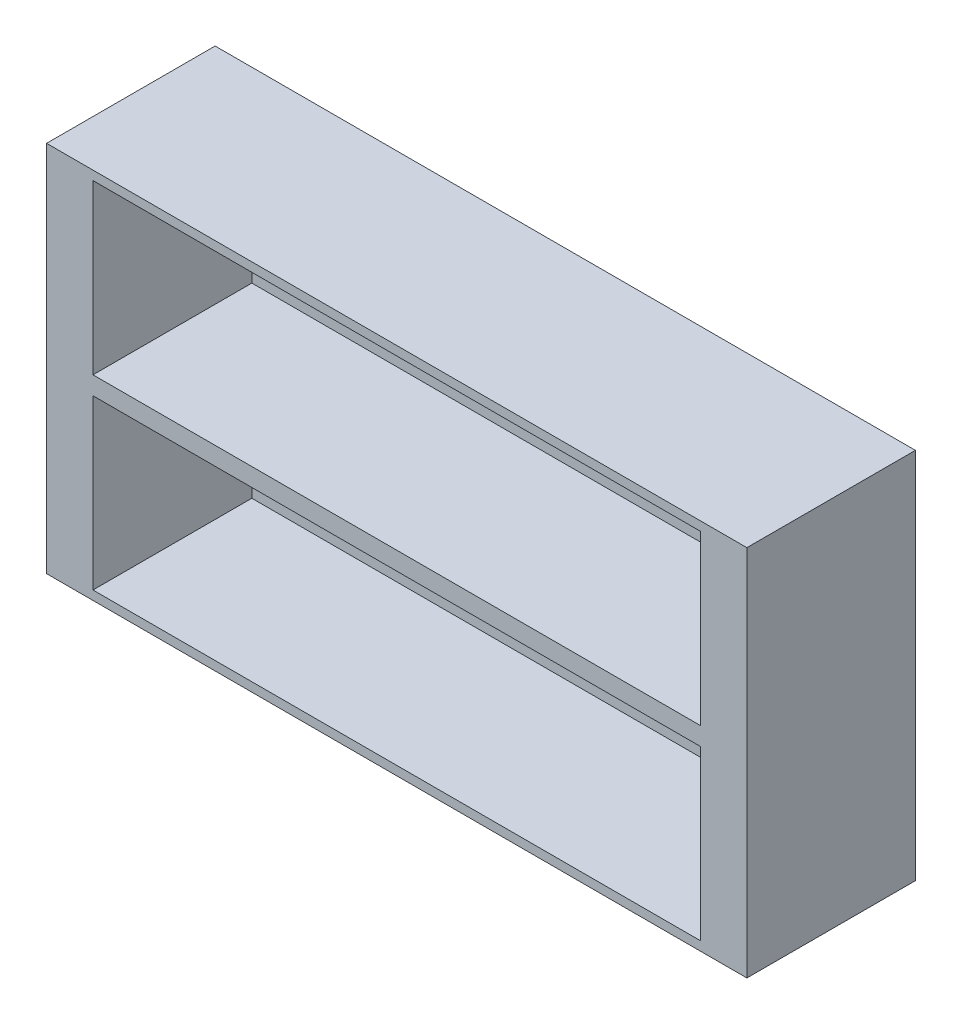
SolidWorks part; units mm, degrees
material "Acrylic (Medium-high impact)"
ref_plane "Front Plane" through (0, 0, 0) normal (0, 0, 1) x (1, 0, 0)
ref_plane "Top Plane" through (0, 0, 0) normal (0, 1, 0) x (1, 0, 0)
ref_plane "Right Plane" through (0, 0, 0) normal (1, 0, 0) x (0, 0, -1)
sketch "Sketch1" plane through (0, 0, 0) normal (0, 0, 1) x (1, 0, 0)
  line L1 (-37.465, -19.939) -> (37.465, -19.939)
  line L2 (-37.465, -19.939) -> (-37.465, 19.939)
  line L3 (-37.465, 19.939) -> (37.465, 19.939)
  line L4 (37.465, -19.939) -> (37.465, 19.939)
  line L5 (-37.465, -19.939) -> (37.465, 19.939) construction
  line L6 (-37.465, 19.939) -> (37.465, -19.939) construction
  point P0 (0, 0)
  dimension "D1" = 39.878
  dimension "D2" = 74.93
extrude "Boss-Extrude1" add sketch "Sketch1" along normal blind 18.034
sketch "Sketch2" plane through (0, 0, 18.034) normal (0, 0, 1) x (1, 0, 0)
  line L0 (0, 0) -> (-14.4056, 0) construction
  circle A0 centre (0, -9.9695) radius 1.5
  circle A1 centre (0, 9.9695) radius 1.5
  dimension "D1" = 3
  dimension "D2" = 9.9695
extrude "Cut-Extrude1" cut sketch "Sketch2" against normal blind 18.034
sketch "Sketch3" plane through (0, 0, 18.034) normal (0, 0, 1) x (1, 0, 0)
  line L0 (0, 0) -> (-28.1693, 0) construction
  line L1 (32.5, 0.9695) -> (-32.5, 0.9695)
  line L2 (32.5, 0.9695) -> (32.5, 18.9695)
  line L3 (32.5, 18.9695) -> (-32.5, 18.9695)
  line L4 (-32.5, 0.9695) -> (-32.5, 18.9695)
  line L5 (32.5, 0.9695) -> (-32.5, 18.9695) construction
  line L6 (32.5, 18.9695) -> (-32.5, 0.9695) construction
  line L7 (32.5, -18.9695) -> (-32.5, -18.9695)
  line L8 (-32.5, -0.9695) -> (-32.5, -18.9695)
  line L9 (32.5, -0.9695) -> (-32.5, -0.9695)
  line L10 (32.5, -0.9695) -> (32.5, -18.9695)
  point P0 (0, 9.9695)
  dimension "D1" = 18
  dimension "D2" = 65
  dimension "D3" = 9.9695
extrude "Cut-Extrude2" cut sketch "Sketch3" against normal blind 17
